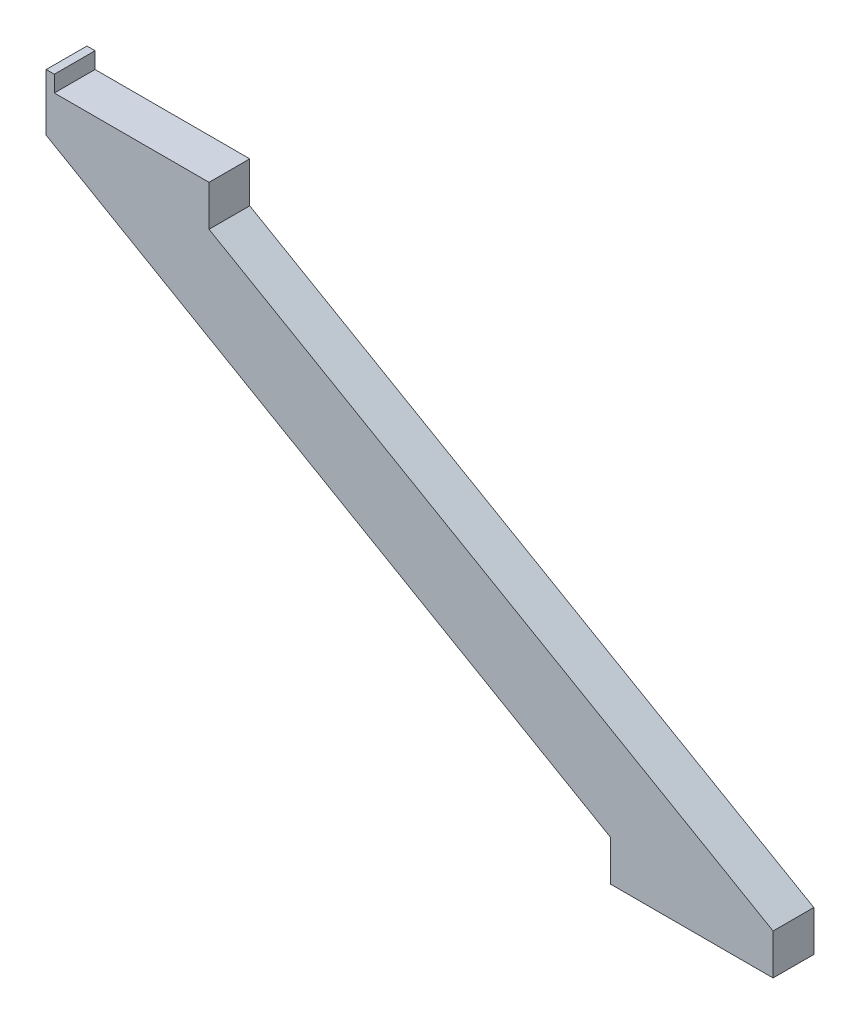
SolidWorks part; units mm, degrees
ref_plane "Front Plane" through (0, 0, 0) normal (0, 0, 1) x (1, 0, 0)
ref_plane "Top Plane" through (0, 0, 0) normal (0, 1, 0) x (1, 0, 0)
ref_plane "Right Plane" through (0, 0, 0) normal (1, 0, 0) x (0, 0, -1)
sketch "Sketch1" plane through (0, 0, 0) normal (0, 0, 1) x (1, 0, 0)
  line L0 (0, 0) -> (100, 0)
  line L1 (100, 0) -> (100, -25)
  line L2 (0, 0) -> (0, -25)
  line L3 (0, -25) -> (346.4102, -225)
  line L5 (446.4102, -225) -> (100, -25)
  line L6 (346.4102, -225) -> (346.4102, -250)
  line L7 (346.4102, -250) -> (446.4102, -250)
  line L8 (446.4102, -250) -> (446.4102, -225)
  point P8 (385.0303, -254.1407)
  point P10 (333.5451, -242.5724)
  dimension "D1" = 100
  dimension "D2" = 100
  dimension "D4" = 25
  dimension "D3" = 25
  dimension "D5" = 30
  dimension "D6" = 250
extrude "Boss-Extrude1" add sketch "Sketch1" along normal blind 25 contours L5 L1 L0 L2 L3 L6 L7 L8
sketch "Sketch2" plane through (0, 0, 0) normal (0, 1, 0) x (1, 0, 0)
  line L0 (0, -25) -> (100, -25) construction
  line L1 (0, 0) -> (5, 0)
  line L2 (0, 0) -> (0, -25)
  line L3 (0, -25) -> (5, -25)
  line L4 (5, 0) -> (5, -25)
  dimension "D1" = 5
extrude "Boss-Extrude2" add sketch "Sketch2" along normal blind 10
equation "\"D2@Sketch1\"=\"D1@Sketch1\""
equation "\"D3@Sketch1\"=\"D4@Sketch1\""
